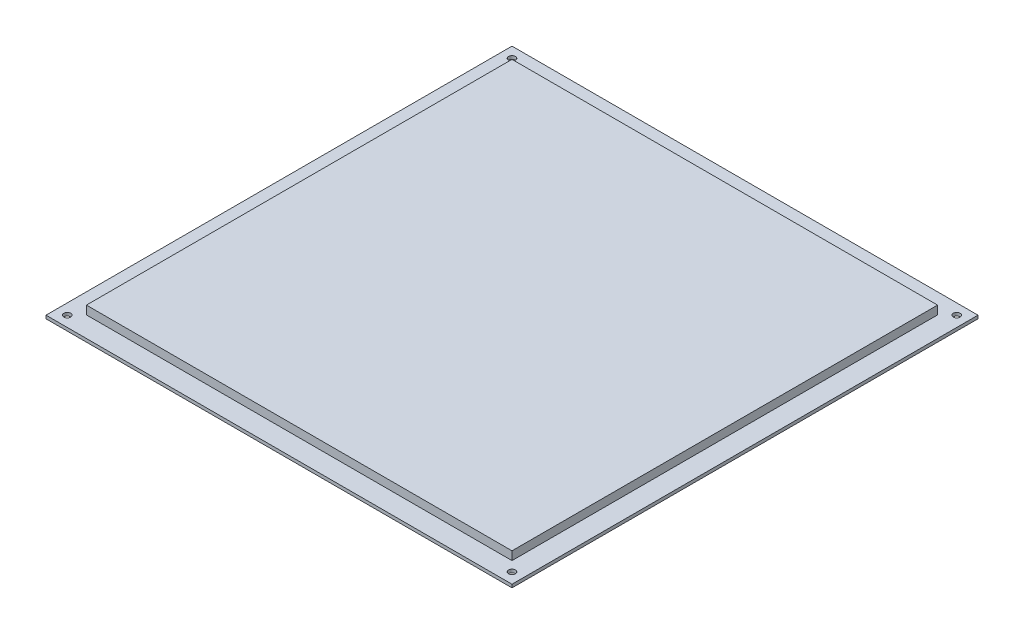
SolidWorks part; units mm, degrees
ref_plane "Front Plane" through (0, 0, 0) normal (0, 0, 1) x (1, 0, 0)
ref_plane "Top Plane" through (0, 0, 0) normal (0, 1, 0) x (1, 0, 0)
ref_plane "Right Plane" through (0, 0, 0) normal (1, 0, 0) x (0, 0, -1)
sketch "Sketch1" plane through (0, 0, 0) normal (0, 1, 0) x (1, 0, 0)
  line L1 (-109.5, 109.5) -> (109.5, 109.5)
  line L2 (-109.5, 109.5) -> (-109.5, -109.5)
  line L3 (-109.5, -109.5) -> (109.5, -109.5)
  line L4 (109.5, 109.5) -> (109.5, -109.5)
  line L5 (-109.5, 109.5) -> (109.5, -109.5) construction
  line L6 (-109.5, -109.5) -> (109.5, 109.5) construction
  point P0 (0, 0)
  dimension "D1" = 219
extrude "Boss-Extrude1" add sketch "Sketch1" along normal blind 1.5
hole_wizard "M3 Clearance Hole1" positions "Sketch3" profile "Sketch2" hole size "M3" standard "ANSI Metric" end condition through all
sketch "Sketch3" plane through (0, 1.5, 0) normal (0, 1, 0) x (1, 0, 0)
  line L1 (-104.5, 104.5) -> (104.5, 104.5) construction
  line L2 (-104.5, 104.5) -> (-104.5, -104.5) construction
  line L3 (-104.5, -104.5) -> (104.5, -104.5) construction
  line L4 (104.5, 104.5) -> (104.5, -104.5) construction
  line L5 (-104.5, 104.5) -> (104.5, -104.5) construction
  line L6 (-104.5, -104.5) -> (104.5, 104.5) construction
  point P0 (-104.5, 104.5)
  point P2 (104.5, 104.5)
  point P4 (104.5, -104.5)
  point P6 (-104.5, -104.5)
  dimension "D1" = 209
sketch "Sketch2" plane through (-104.5, 1.5, -104.5) normal (1, 0, 0) x (0, 0, 1)
  line L0 (0, 0) -> (0, 1.5)
  line L1 (0, 1.5) -> (1.6, 1.5)
  line L2 (1.6, 1.5) -> (1.6, 0)
  line L5 (1.6, 0) -> (0, 0)
  line L11 (0, -6.35) -> (0, 107.95) construction
  dimension "Thru Hole Dia." = 3.2
  dimension "Thru Hole Depth" = 1.5
ref_plane "Plane2" through (0, 1.6, 0) normal (0, 1, 0) x (1, 0, 0)
sketch "Sketch5" plane through (0, 1.6, 0) normal (0, 1, 0) x (1, 0, 0)
  line L1 (-100, 100) -> (100, 100)
  line L2 (-100, 100) -> (-100, -100)
  line L3 (-100, -100) -> (100, -100)
  line L4 (100, 100) -> (100, -100)
  line L5 (-100, 100) -> (100, -100) construction
  line L6 (-100, -100) -> (100, 100) construction
  point P0 (0, 0)
  dimension "D1" = 200
extrude "Boss-Extrude2" add sketch "Sketch5" along normal blind 4 separate body
